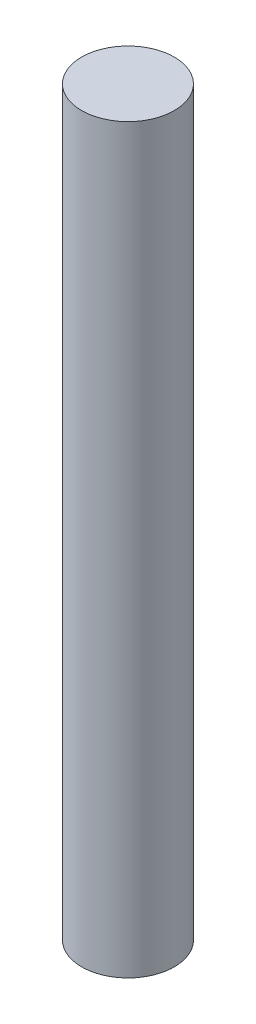
SolidWorks part; units mm, degrees
material "1060 Alloy"
ref_plane "Front Plane" through (0, 0, 0) normal (0, 0, 1) x (1, 0, 0)
ref_plane "Top Plane" through (0, 0, 0) normal (0, 1, 0) x (1, 0, 0)
ref_plane "Right Plane" through (0, 0, 0) normal (1, 0, 0) x (0, 0, -1)
sketch "Sketch1" plane through (0, 0, 0) normal (0, 0, 1) x (1, 0, 0)
  line L0 (0, 101.6) -> (0, -101.6) construction
  line L1 (0, 76.2) -> (9.525, 76.2)
  line L2 (9.525, 76.2) -> (9.525, -76.2)
  line L3 (9.525, -76.2) -> (0, -76.2)
  line L4 (0, 76.2) -> (0, -76.2)
  point P5 (9.525, 0)
  dimension "D2" = 19.05
revolve "Revolve1" add sketch "Sketch1" angle 360 about L0
equation "\"Rod Diameter\"= 0.75in'This will remain constant in the steering column"
equation "\"Rod Length\"= 6in'This might change for different rods in steering column"
equation "\"D1@Sketch1\"= \"Rod Length\""
equation "\"D2@Sketch1\"=\"Rod Diameter\""
